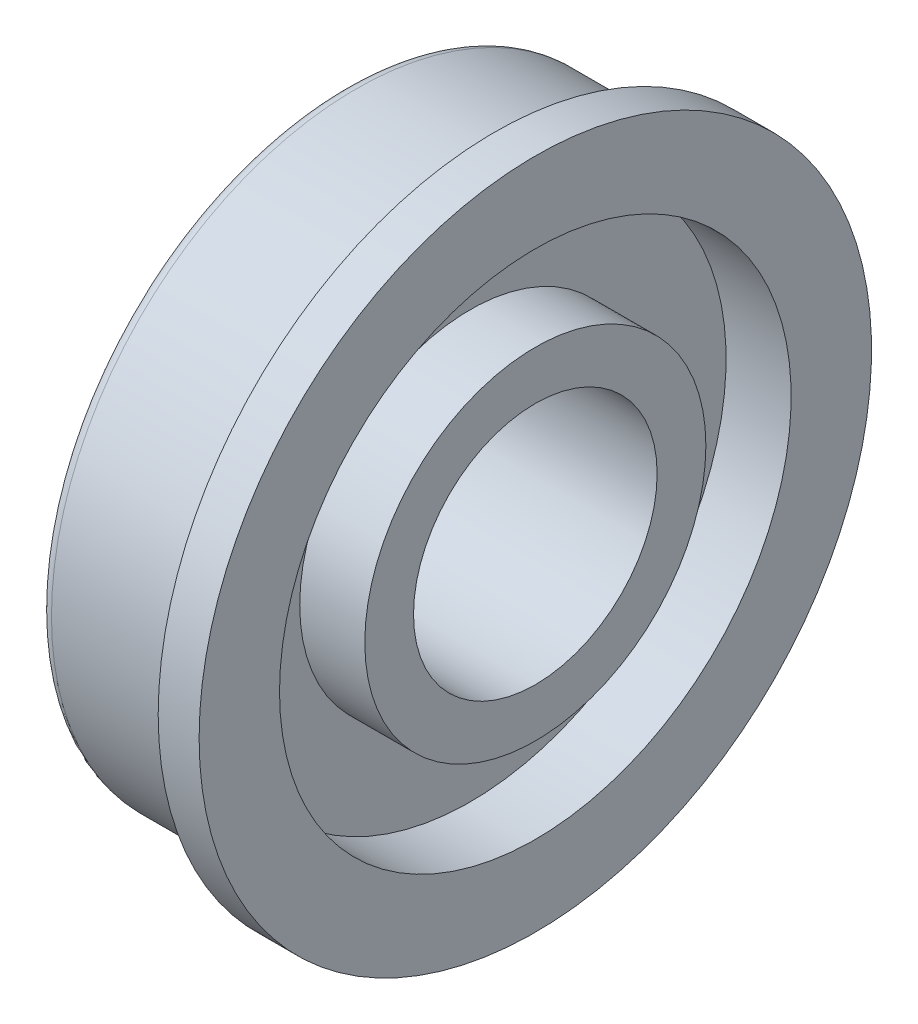
SolidWorks part; units mm, degrees
ref_plane "Front" through (0, 0, 0) normal (0, 0, 1) x (1, 0, 0)
ref_plane "Top" through (0, 0, 0) normal (0, 1, 0) x (1, 0, 0)
ref_plane "Right" through (0, 0, 0) normal (1, 0, 0) x (0, 0, -1)
sketch "Sketch3" plane through (0, 0, 0) normal (0, 0, 1) x (1, 0, 0)
  line L0 (-4.8321, 0) -> (5.0556, 0) construction
  line L1 (0.3048, 3.175) -> (4.9784, 3.175)
  line L2 (4.9784, 3.175) -> (4.9784, 4.445)
  line L3 (4.9784, 4.445) -> (3.2829, 4.445)
  line L4 (3.2829, 4.445) -> (3.283, 6.6675)
  line L5 (3.283, 6.6675) -> (4.9784, 6.6675)
  line L6 (4.9784, 6.6675) -> (4.9784, 8.763)
  line L7 (4.9784, 8.763) -> (3.9116, 8.763)
  line L8 (3.9116, 8.763) -> (3.9116, 7.9375)
  line L9 (3.9116, 7.9375) -> (0.3048, 7.9375)
  line L10 (0, 7.6327) -> (0, 6.6675)
  line L11 (0, 6.6675) -> (1.6955, 6.6675)
  line L12 (1.6955, 6.6675) -> (1.6954, 4.445)
  line L13 (1.6954, 4.445) -> (0, 4.445)
  line L14 (0, 4.445) -> (0, 3.4798)
  line L15 (0, 3.175) -> (0, 0) construction
  arc A0 (0, 3.4798) -> (0.3048, 3.175) centre (0.3048, 3.4798) ccw
  arc A1 (0.3048, 7.9375) -> (0, 7.6327) centre (0.3048, 7.6327) ccw
  point P23 (0, 7.9375)
  dimension "R" = 0.3048
  dimension "T" = 1.0668
  dimension "ID" = 6.35
  dimension "F" = 17.526
  dimension "OD" = 15.875
  dimension "W" = 4.9784
  dimension "BALLDIA" = 1.5875
  dimension "IRT" = 1.27
  dimension "ORT" = 1.27
revolve "bearing-revolution" add sketch "Sketch3" angle 360 about L0
